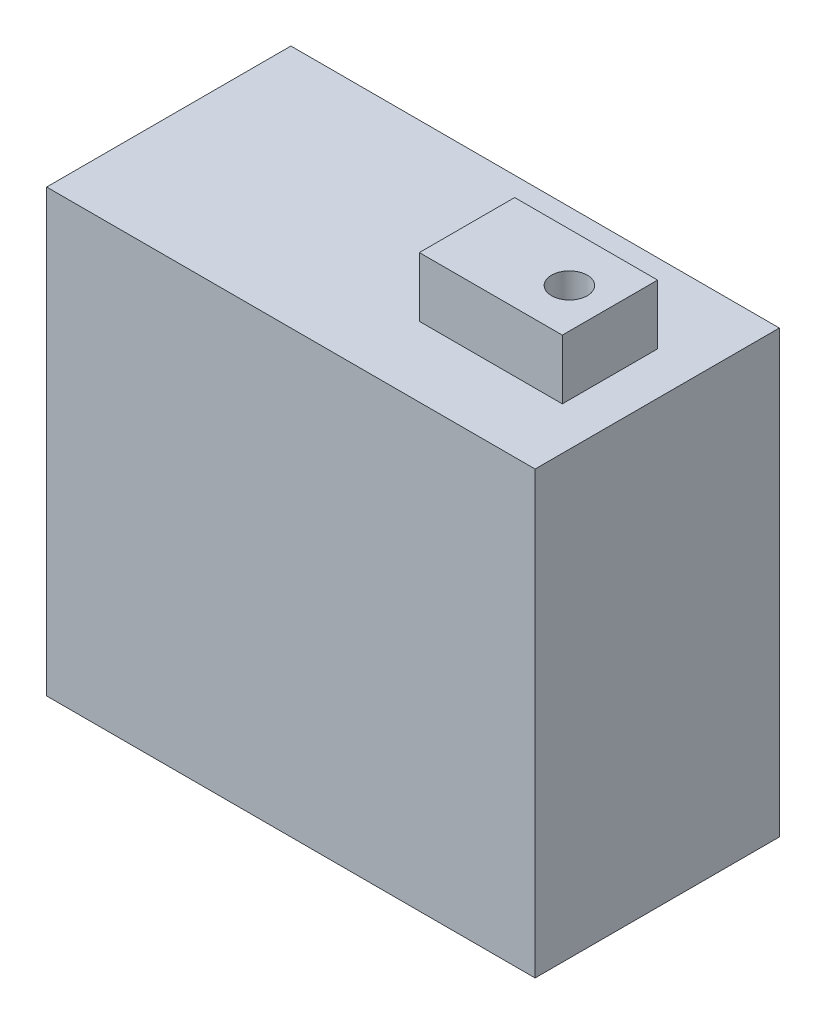
SolidWorks part; units mm, degrees
material "Rubber"
ref_plane "Front Plane" through (0, 0, 0) normal (0, 0, 1) x (1, 0, 0)
ref_plane "Top Plane" through (0, 0, 0) normal (0, 1, 0) x (1, 0, 0)
ref_plane "Right Plane" through (0, 0, 0) normal (1, 0, 0) x (0, 0, -1)
sketch "Sketch3" plane through (0, 0, 0) normal (0, 1, 0) x (1, 0, 0)
  line L1 (0, 0) -> (41, 0)
  line L2 (0, 0) -> (0, 20.5)
  line L3 (0, 20.5) -> (41, 20.5)
  line L4 (41, 0) -> (41, 20.5)
  dimension "D1" = 20.5
  dimension "D2" = 41
extrude "Boss-Extrude1" add sketch "Sketch3" along normal blind 37
sketch "Sketch5" plane through (0, 37, 0) normal (0, 1, 0) x (1, 0, 0)
  line L1 (25.4068, 5.8762) -> (37.4068, 5.8762)
  line L2 (25.4068, 5.8762) -> (25.4068, 13.8762)
  line L3 (25.4068, 13.8762) -> (37.4068, 13.8762)
  line L4 (37.4068, 5.8762) -> (37.4068, 13.8762)
  line L5 (25.4068, 5.8762) -> (37.4068, 13.8762) construction
  line L6 (25.4068, 13.8762) -> (37.4068, 5.8762) construction
  point P0 (31.4068, 9.8762)
  dimension "D1" = 12
  dimension "D2" = 8
extrude "Boss-Extrude2" add sketch "Sketch5" along normal blind 5
sketch "Sketch6" plane through (0, 42, 0) normal (0, 1, 0) x (1, 0, 0)
  circle A0 centre (34.0954, 9.7833) radius 1.5
  dimension "D1" = 3
extrude "Cut-Extrude1" cut sketch "Sketch6" against normal blind 30
